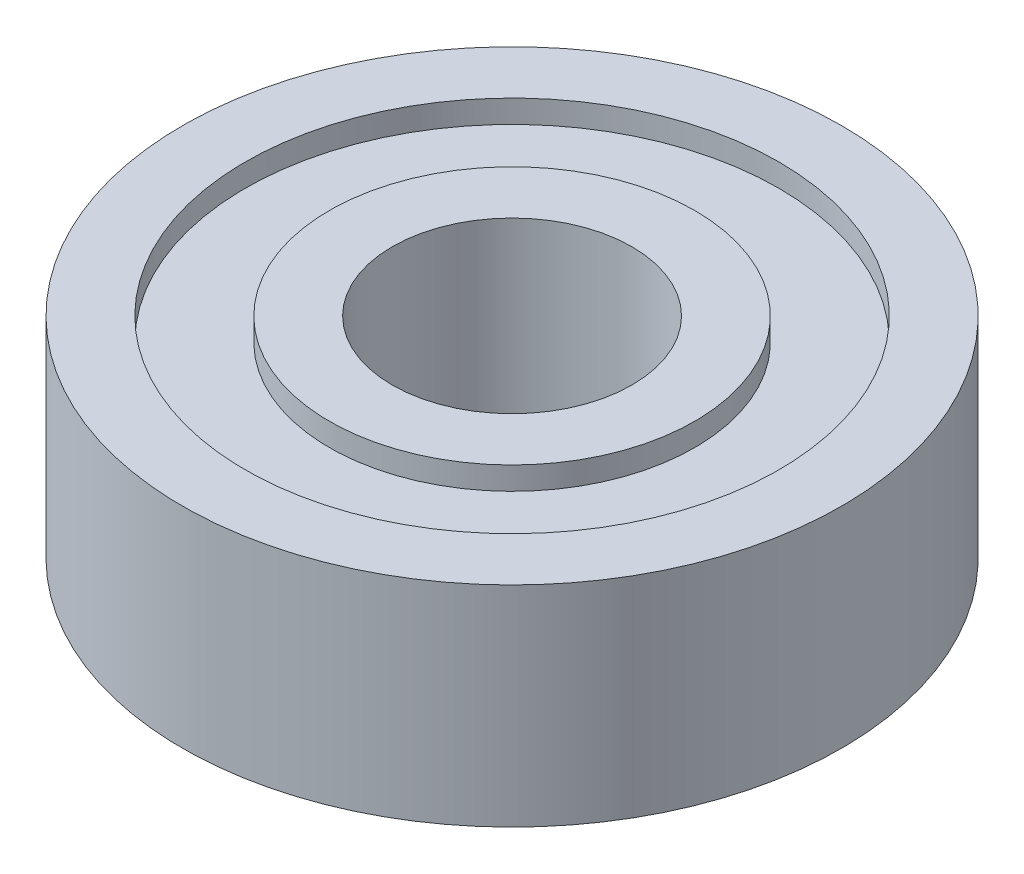
SolidWorks part; units mm, degrees
material "Bearing material"
ref_plane "Front Plane" through (0, 0, 0) normal (0, 0, 1) x (1, 0, 0)
ref_plane "Top Plane" through (0, 0, 0) normal (0, 1, 0) x (1, 0, 0)
ref_plane "Right Plane" through (0, 0, 0) normal (1, 0, 0) x (0, 0, -1)
sketch "Sketch1" plane through (0, 0, 0) normal (0, 0, 1) x (1, 0, 0)
  line L0 (0, 0) -> (0, 16.369) construction
  line L1 (0, 0) -> (24.8515, 0) construction
  line L2 (11, -3.5) -> (11, 3.5)
  line L3 (11, 3.5) -> (8.904, 3.5)
  line L4 (8.904, 3.5) -> (8.904, 2.738)
  line L5 (8.904, 2.738) -> (6.096, 2.738)
  line L6 (6.096, 2.738) -> (6.096, 3.5)
  line L7 (6.096, 3.5) -> (4, 3.5)
  line L8 (4, 3.5) -> (4, -3.5)
  line L9 (6.096, -3.5) -> (4, -3.5)
  line L10 (6.096, -2.738) -> (6.096, -3.5)
  line L11 (8.904, -2.738) -> (6.096, -2.738)
  line L12 (8.904, -3.5) -> (8.904, -2.738)
  line L13 (11, -3.5) -> (8.904, -3.5)
  point P13 (11, 0)
  point P14 (4, 0)
  dimension "D1" = 22
  dimension "D2" = 8
  dimension "D3" = 7
  dimension "D4" = 6.096
  dimension "D5" = 0.762
revolve "Revolve1" add sketch "Sketch1" angle 360 about L0
